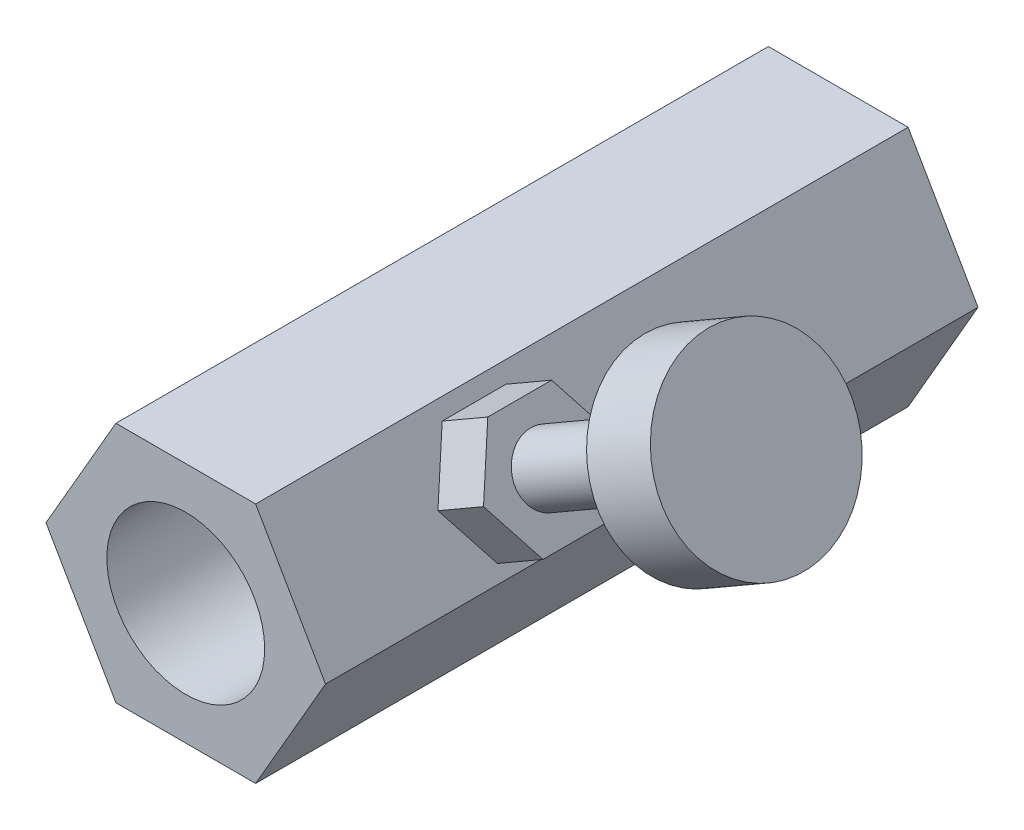
SolidWorks part; units mm, degrees
ref_plane "前视基准面" through (0, 0, 0) normal (0, 0, 1) x (1, 0, 0)
ref_plane "上视基准面" through (0, 0, 0) normal (0, 1, 0) x (1, 0, 0)
ref_plane "右视基准面" through (0, 0, 0) normal (1, 0, 0) x (0, 0, -1)
sketch "草图1" plane through (0, 0, 0) normal (0, 0, 1) x (1, 0, 0)
  line L0 (-6.6395, -11.5) -> (6.6395, -11.5)
  line L1 (6.6395, -11.5) -> (13.2791, 0)
  line L2 (13.2791, 0) -> (6.6395, 11.5)
  line L3 (6.6395, 11.5) -> (-6.6395, 11.5)
  line L4 (-6.6395, 11.5) -> (-13.2791, 0)
  line L5 (-13.2791, 0) -> (-6.6395, -11.5)
  line L6 (6.6395, 11.5) -> (-6.6395, -11.5) construction
  line L7 (-13.2791, 0) -> (0, 0) construction
  circle A0 centre (0, 0) radius 11.5 construction
  dimension "D1" = 23
extrude "凸台-拉伸1" add sketch "草图1" along normal blind 20 and the other way blind 42
sketch "草图2" plane through (0, 0, 20) normal (0, 0, 1) x (1, 0, 0)
  circle A0 centre (0, 0) radius 7.5
  dimension "D1" = 15
extrude "切除-拉伸1" cut sketch "草图2" against normal blind 65
sketch "草图3" plane through (9.9593, 5.75, 0) normal (0.866, 0.5, 0) x (0, 0, -1)
  line L0 (-3.0206, -5.3572) -> (3.0416, -5.3572)
  line L1 (3.0416, -5.3572) -> (6.0727, -0.1072)
  line L2 (6.0727, -0.1072) -> (3.0416, 5.1428)
  line L3 (3.0416, 5.1428) -> (-3.0206, 5.1428)
  line L4 (-3.0206, 5.1428) -> (-6.0517, -0.1072)
  line L5 (-6.0517, -0.1072) -> (-3.0206, -5.3572)
extrude "凸台-拉伸2" add sketch "草图3" along normal blind 5
sketch "草图4" plane through (14.2894, 8.25, 0) normal (0.866, 0.5, 0) x (0, 0, -1)
  circle A0 centre (0, 0) radius 3
  dimension "D1" = 6
extrude "凸台-拉伸3" add sketch "草图4" along normal blind 16
sketch "草图5" plane through (28.1458, 16.25, 0) normal (0.866, 0.5, 0) x (0, 0, -1)
  circle A0 centre (0, 0) radius 9
  dimension "D1" = 18
extrude "凸台-拉伸4" add sketch "草图5" along normal blind 7
sketch "草图6" plane through (-9.9593, -5.75, 0) normal (-0.866, -0.5, 0) x (0, 0, 1)
  line L0 (-16.7322, -5.46) -> (-10.4275, -5.46)
  line L1 (-10.4275, -5.46) -> (-7.2752, 0)
  line L2 (-7.2752, 0) -> (-10.4275, 5.46)
  line L3 (-10.4275, 5.46) -> (-16.7322, 5.46)
  line L4 (-16.7322, 5.46) -> (-19.8845, 0)
  line L5 (-19.8845, 0) -> (-16.7322, -5.46)
extrude "凸台-拉伸5" add sketch "草图6" along normal blind 7
